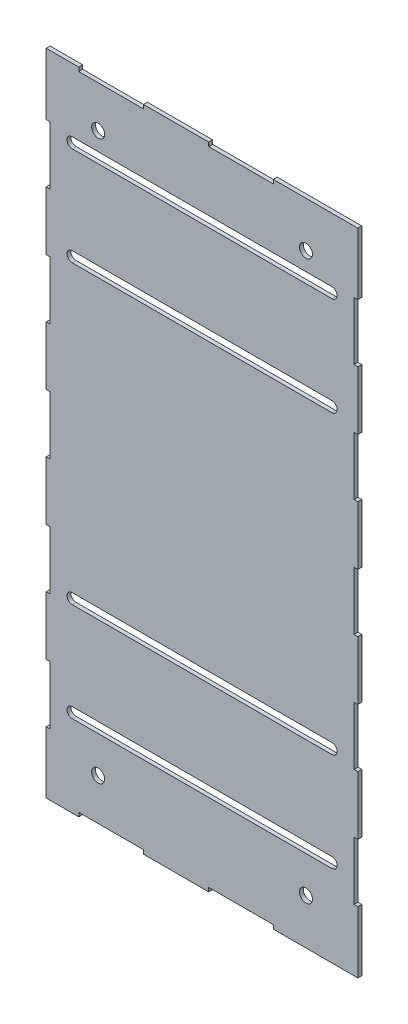
SolidWorks part; units mm, degrees
ref_plane "Alzado" through (0, 0, 0) normal (0, 0, 1) x (1, 0, 0)
ref_plane "Planta" through (0, 0, 0) normal (0, 1, 0) x (1, 0, 0)
ref_plane "Vista lateral" through (0, 0, 0) normal (1, 0, 0) x (0, 0, -1)
sketch "Croquis1" plane through (0, 0, 0) normal (0, 0, 1) x (1, 0, 0)
  line L0 (-100, 197) -> (100, 197) construction
  line L1 (-120, 250) -> (120, 250)
  line L2 (-120, 250) -> (-120, -250)
  line L3 (-120, -250) -> (120, -250)
  line L4 (120, 250) -> (120, -250)
  line L5 (-120, 250) -> (120, -250) construction
  line L6 (-120, -250) -> (120, 250) construction
  line L7 (-100, 201) -> (100, 201)
  line L8 (-100, 193) -> (100, 193)
  line L9 (-100, 117) -> (100, 117)
  line L10 (-100, 125) -> (100, 125)
  line L11 (-100, 121) -> (100, 121) construction
  line L20 (0, 250) -> (0, 163.6039) construction
  line L25 (0, 0) -> (-80, 0) construction
  line L26 (-100, -111) -> (100, -111)
  line L27 (-100, -103) -> (100, -103)
  line L28 (-100, -107) -> (100, -107) construction
  line L29 (-100, -187) -> (100, -187)
  line L30 (-100, -179) -> (100, -179)
  line L31 (-100, -183) -> (100, -183) construction
  line L32 (-100, 49) -> (100, 49) [skipped]
  line L33 (-100, 41) -> (100, 41) [skipped]
  line L34 (-100, -27) -> (100, -27) [skipped]
  line L35 (-100, -35) -> (100, -35) [skipped]
  line L48 (0, 0) -> (0, -70.2639) construction
  arc A0 (-100, 201) -> (-100, 193) centre (-100, 197) ccw
  arc A1 (100, 193) -> (100, 201) centre (100, 197) ccw
  arc A10 (-100, 125) -> (-100, 117) centre (-100, 121) ccw
  arc A11 (100, 117) -> (100, 125) centre (100, 121) ccw
  arc A16 (-100, -103) -> (-100, -111) centre (-100, -107) ccw
  arc A17 (100, -111) -> (100, -103) centre (100, -107) ccw
  arc A18 (-100, -179) -> (-100, -187) centre (-100, -183) ccw
  arc A19 (100, -187) -> (100, -179) centre (100, -183) ccw
  arc A20 (-100, 49) -> (-100, 41) centre (-100, 45) ccw [skipped]
  arc A21 (100, 41) -> (100, 49) centre (100, 45) ccw [skipped]
  arc A22 (-100, -27) -> (-100, -35) centre (-100, -31) ccw [skipped]
  arc A23 (100, -35) -> (100, -27) centre (100, -31) ccw [skipped]
  circle A32 centre (-80, -215) radius 5
  circle A34 centre (80, -215) radius 5
  circle A36 centre (80, 215) radius 5
  circle A37 centre (-80, 215) radius 5
  point P0 (0, 0)
  point P8 (0, 197)
  point P17 (0, 121)
  point P38 (0, -107)
  point P45 (0, -183)
  dimension "D5" = 200
  dimension "D10" = 10
  dimension "D1" = 500
  dimension "D2" = 240
  dimension "D3" = 8
  dimension "D4" = 49
  dimension "D6" = 20
  dimension "D8" = 6
  dimension "D7" = 76
  dimension "D9" = 40
  dimension "D11" = 35
extrude "Saliente-Extruir1" add sketch "Croquis1" along normal blind 3
sketch "Croquis5" plane through (0, 0, 0) normal (0, 0, -1) x (-1, 0, 0)
  line L0 (120, 250) -> (-120, 250) construction
  line L1 (120, 250) -> (120, -250) construction
  line L2 (-54.9, 250) -> (-54.9, 247)
  line L3 (-54.9, 247) -> (-5.1, 247)
  line L28 (-5.1, 247) -> (-5.1, 250)
  line L29 (-5.1, 250) -> (-54.9, 250)
  line L30 (-154.9, 250) -> (-154.9, 247) construction
  line L31 (-154.9, 247) -> (-105.1, 247) construction
  line L32 (45.1, 250) -> (45.1, 247)
  line L33 (45.1, 247) -> (94.9, 247)
  line L34 (94.9, 247) -> (94.9, 250)
  line L35 (94.9, 250) -> (45.1, 250)
  line L52 (-105.1, 247) -> (-105.1, 250) construction
  line L53 (-105.1, 250) -> (-154.9, 250) construction
  line L54 (-254.9, 250) -> (-254.9, 247) construction
  line L55 (-254.9, 247) -> (-205.1, 247) construction
  line L148 (-205.1, 247) -> (-205.1, 250) construction
  line L149 (-205.1, 250) -> (-254.9, 250) construction
  line L150 (-354.9, 250) -> (-354.9, 247) construction
  line L151 (-354.9, 247) -> (-305.1, 247) construction
  line L152 (117, 202.4) -> (117, 157.6)
  line L153 (117, 157.6) -> (120, 157.6)
  line L154 (120, 157.6) -> (120, 202.4)
  line L155 (120, 202.4) -> (117, 202.4)
  line L156 (-305.1, 247) -> (-305.1, 250) construction
  line L157 (-305.1, 250) -> (-354.9, 250) construction
  line L158 (-454.9, 250) -> (-454.9, 247) construction
  line L159 (-454.9, 247) -> (-405.1, 247) construction
  line L160 (-405.1, 247) -> (-405.1, 250) construction
  line L161 (-405.1, 250) -> (-454.9, 250) construction
  line L182 (117, 112.4) -> (117, 67.6)
  line L183 (117, 67.6) -> (120, 67.6)
  line L184 (120, 67.6) -> (120, 112.4)
  line L185 (120, 112.4) -> (117, 112.4)
  line L186 (117, 22.4) -> (117, -22.4)
  line L187 (117, -22.4) -> (120, -22.4)
  line L188 (120, -22.4) -> (120, 22.4)
  line L189 (120, 22.4) -> (117, 22.4)
  line L190 (117, -67.6) -> (117, -112.4)
  line L191 (117, -112.4) -> (120, -112.4)
  line L192 (120, -112.4) -> (120, -67.6)
  line L193 (120, -67.6) -> (117, -67.6)
  line L194 (117, -157.6) -> (117, -202.4)
  line L195 (117, -202.4) -> (120, -202.4)
  line L196 (120, -202.4) -> (120, -157.6)
  line L197 (120, -157.6) -> (117, -157.6)
  line L198 (0, 0) -> (0, 89.4251) construction
  line L199 (0, 0) -> (95.335, 0) construction
  line L200 (-405.1, -250) -> (-454.9, -250) construction
  line L201 (-405.1, -247) -> (-405.1, -250) construction
  line L202 (-454.9, -247) -> (-405.1, -247) construction
  line L203 (-454.9, -250) -> (-454.9, -247) construction
  line L204 (-305.1, -250) -> (-354.9, -250) construction
  line L205 (-305.1, -247) -> (-305.1, -250) construction
  line L206 (-354.9, -247) -> (-305.1, -247) construction
  line L207 (-354.9, -250) -> (-354.9, -247) construction
  line L208 (-205.1, -250) -> (-254.9, -250) construction
  line L209 (-205.1, -247) -> (-205.1, -250) construction
  line L210 (-254.9, -247) -> (-205.1, -247) construction
  line L211 (-254.9, -250) -> (-254.9, -247) construction
  line L212 (-105.1, -250) -> (-154.9, -250) construction
  line L213 (-105.1, -247) -> (-105.1, -250) construction
  line L214 (94.9, -250) -> (45.1, -250)
  line L215 (94.9, -247) -> (94.9, -250)
  line L216 (45.1, -247) -> (94.9, -247)
  line L217 (45.1, -250) -> (45.1, -247)
  line L218 (-154.9, -247) -> (-105.1, -247) construction
  line L219 (-154.9, -250) -> (-154.9, -247) construction
  line L220 (-5.1, -250) -> (-54.9, -250)
  line L221 (-5.1, -247) -> (-5.1, -250)
  line L222 (-54.9, -247) -> (-5.1, -247)
  line L223 (-54.9, -250) -> (-54.9, -247)
  line L224 (-120, -157.6) -> (-117, -157.6)
  line L225 (-120, -202.4) -> (-120, -157.6)
  line L226 (-117, -202.4) -> (-120, -202.4)
  line L227 (-117, -157.6) -> (-117, -202.4)
  line L228 (-120, -67.6) -> (-117, -67.6)
  line L229 (-120, -112.4) -> (-120, -67.6)
  line L230 (-117, -112.4) -> (-120, -112.4)
  line L231 (-117, -67.6) -> (-117, -112.4)
  line L232 (-120, 22.4) -> (-117, 22.4)
  line L233 (-120, -22.4) -> (-120, 22.4)
  line L234 (-117, -22.4) -> (-120, -22.4)
  line L235 (-117, 22.4) -> (-117, -22.4)
  line L236 (-120, 112.4) -> (-117, 112.4)
  line L237 (-120, 67.6) -> (-120, 112.4)
  line L238 (-117, 67.6) -> (-120, 67.6)
  line L239 (-117, 112.4) -> (-117, 67.6)
  line L240 (-120, 202.4) -> (-117, 202.4)
  line L241 (-120, 157.6) -> (-120, 202.4)
  line L242 (-117, 157.6) -> (-120, 157.6)
  line L243 (-117, 202.4) -> (-117, 157.6)
  dimension "D1" = 47.6
  dimension "D2" = 44.8
  dimension "D3" = 3
  dimension "D4" = 25.1
  dimension "D5" = 49.8
  dimension "D6" = 3
  dimension "D8" = 50.2
  dimension "D9" = 45.2
  dimension "D7" = 6
  dimension "D10" = 5
extrude "Cortar-Extruir2" cut sketch "Croquis5" against normal through all
